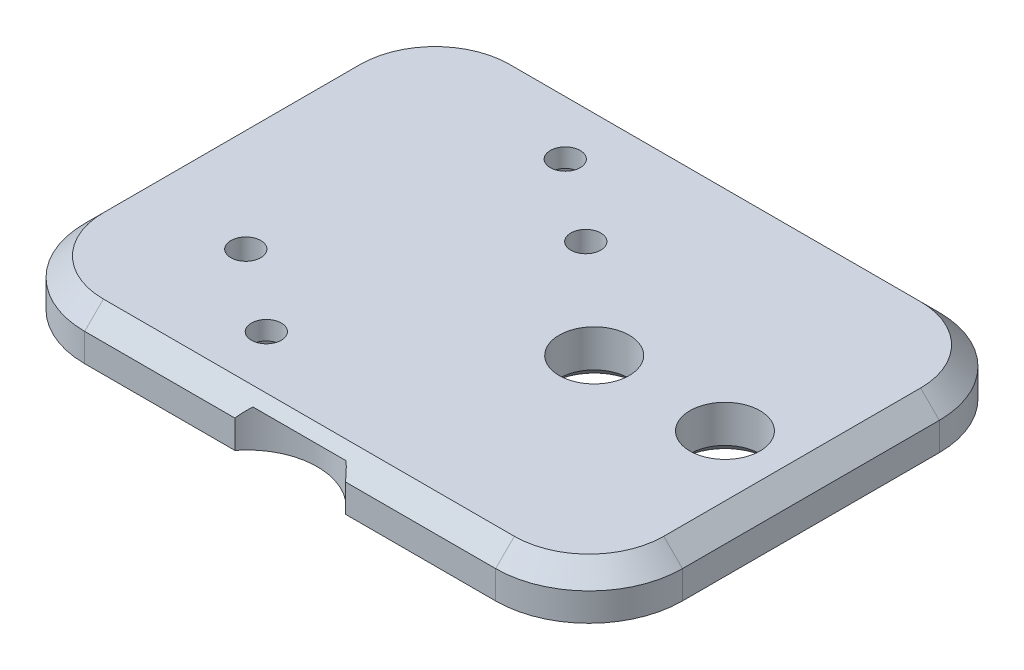
SolidWorks part; units mm, degrees
ref_plane "Front Plane" through (0, 0, 0) normal (0, 0, 1) x (1, 0, 0)
ref_plane "Top Plane" through (0, 0, 0) normal (0, 1, 0) x (1, 0, 0)
ref_plane "Right Plane" through (0, 0, 0) normal (1, 0, 0) x (0, 0, -1)
sketch "Sketch1" plane through (0, 0, 0) normal (0, 1, 0) x (1, 0, 0)
  line L0 (-37.5919, -19.2294) -> (-37.5919, -66.7294) construction
  line L1 (-69.5919, -19.2294) -> (-5.5919, -19.2294)
  line L2 (-69.5919, -19.2294) -> (-69.5919, -66.7294)
  line L3 (-69.5919, -66.7294) -> (-5.5919, -66.7294)
  line L4 (-5.5919, -19.2294) -> (-5.5919, -66.7294)
  line L5 (-69.5919, -19.2294) -> (-5.5919, -66.7294) construction
  line L6 (-69.5919, -66.7294) -> (-5.5919, -19.2294) construction
  line L8 (-59.5919, -19.2294) -> (-15.5919, -19.2294) construction
  line L9 (-5.5919, -29.2294) -> (-5.5919, -66.7294) construction
  circle A0 centre (-39.0919, -33.5794) radius 1.6
  circle A1 centre (-56.5919, -52.4794) radius 1.6
  circle A2 centre (-28.0919, -43.6794) radius 3.75
  circle A3 centre (-14.0919, -43.6794) radius 3.75
  point P0 (0, 0)
  dimension "D1" = 3.2
  dimension "D2" = 3.2
  dimension "D3" = 7.5
  dimension "D4" = 7.5
extrude "Boss-Extrude1" add sketch "Sketch1" along normal blind 5
sketch "Sketch2" plane through (0, 0, 0) normal (0, -1, 0) x (1, 0, 0)
  line L0 (-47.8419, 59.0294) -> (-47.8419, 27.0294) construction
  line L1 (-56.5919, 52.4794) -> (-39.0919, 33.5794) construction
  line L2 (-5.5919, 43.6794) -> (-69.5919, 43.6794) construction
  line L3 (-5.5919, 66.7294) -> (-5.5919, 19.2294) construction
  line L4 (-69.5919, 19.2294) -> (-69.5919, 66.7294) construction
  line L5 (-29.5919, 43.6794) -> (-26.5919, 43.6794) construction
  line L6 (-52.8419, 22.0294) -> (-42.8419, 22.0294) construction
  line L7 (-52.8419, 22.0294) -> (-52.8419, 64.0294) construction
  line L8 (-52.8419, 64.0294) -> (-42.8419, 64.0294) construction
  line L9 (-42.8419, 22.0294) -> (-42.8419, 64.0294) construction
  line L10 (-52.8419, 22.0294) -> (-42.8419, 64.0294) construction
  line L11 (-52.8419, 64.0294) -> (-42.8419, 22.0294) construction
  circle A0 centre (-47.8419, 59.0294) radius 1.6
  circle A3 centre (-47.8419, 27.0294) radius 1.6
  circle A4 centre (-28.0919, 43.6794) radius 1.5 construction
  point P5 (-47.8419, 43.0294)
  dimension "D1" = 3.2
  dimension "D2" = 10
  dimension "D3" = 5
  dimension "D4" = 3.2
  dimension "D5" = 32
extrude "Cut-Extrude1" cut sketch "Sketch2" against normal through all
sketch "Sketch3" plane through (0, 0, 0) normal (0, -1, 0) x (-1, 0, 0)
  line L1 (49.4296, -56.2794) -> (46.2542, -56.2794)
  line L2 (46.2542, -56.2794) -> (44.6665, -59.0294)
  line L3 (44.6665, -59.0294) -> (46.2542, -61.7794)
  line L4 (46.2542, -61.7794) -> (49.4296, -61.7794)
  line L5 (49.4296, -61.7794) -> (51.0173, -59.0294)
  line L6 (51.0173, -59.0294) -> (49.4296, -56.2794)
  line L18 (46.2542, -29.7794) -> (49.4296, -29.7794)
  line L19 (49.4296, -29.7794) -> (51.0173, -27.0294)
  line L20 (51.0173, -27.0294) -> (49.4296, -24.2794)
  line L21 (49.4296, -24.2794) -> (46.2542, -24.2794)
  line L22 (46.2542, -24.2794) -> (44.6665, -27.0294)
  line L23 (44.6665, -27.0294) -> (46.2542, -29.7794)
  line L30 (34.5919, -44.6171) -> (34.5919, -41.4417) [skipped]
  line L31 (34.5919, -41.4417) -> (31.8419, -39.854) [skipped]
  line L32 (31.8419, -39.854) -> (29.0919, -41.4417) [skipped]
  line L33 (29.0919, -41.4417) -> (29.0919, -44.6171) [skipped]
  line L34 (29.0919, -44.6171) -> (31.8419, -46.2048) [skipped]
  line L35 (31.8419, -46.2048) -> (34.5919, -44.6171) [skipped]
  line L36 (61.0919, -41.4417) -> (61.0919, -44.6171) [skipped]
  line L37 (61.0919, -44.6171) -> (63.8419, -46.2048) [skipped]
  line L38 (63.8419, -46.2048) -> (66.5919, -44.6171) [skipped]
  line L39 (66.5919, -44.6171) -> (66.5919, -41.4417) [skipped]
  line L40 (66.5919, -41.4417) -> (63.8419, -39.854) [skipped]
  line L41 (63.8419, -39.854) -> (61.0919, -41.4417) [skipped]
  circle A0 centre (47.8419, -59.0294) radius 2.75 construction
  circle A2 centre (47.8419, -27.0294) radius 2.75 construction
  circle A3 centre (47.8419, -27.0294) radius 1.6 construction
  circle A5 centre (31.8419, -43.0294) radius 2.75 construction
  circle A6 centre (63.8419, -43.0294) radius 2.75 construction
  dimension "D2" = 5.5
  dimension "D1" = 4
extrude "Cut-Extrude2" cut sketch "Sketch3" against normal blind 3
fillet "Fillet1" radius 10 2 edges at (-5.5919, 2.5, 19.2294) (-69.5919, 2.5, 19.2294)
fillet "Fillet2" radius 10 2 edges at (-5.5919, 2.5, 66.7294) (-69.5919, 2.5, 66.7294)
chamfer "Chamfer1" distance 2 angle 45 8 edges at (-5.5919, 5, 42.9794) (-69.5919, 5, 42.9794) (-8.5209, 5, 22.1583) (-66.663, 5, 22.1583) (-37.5919, 5, 19.2294) (-37.5919, 5, 66.7294) (-8.5209, 5, 63.8005) (-66.663, 5, 63.8005)
chamfer "Chamfer2" distance 1 angle 45 2 edges at (-28.0919, 0, 47.4294) (-14.0919, 0, 47.4294)
sketch "Sketch4" plane through (0, 0, 0) normal (0, 1, 0) x (1, 0, 0)
  line L0 (-37.5919, -19.2294) -> (-37.5919, -66.7294) construction
  line L1 (-15.5919, -19.2294) -> (-59.5919, -19.2294) construction
  line L2 (-59.5919, -66.7294) -> (-15.5919, -66.7294) construction
  circle A0 centre (-57.5919, -31.1294) radius 5.25
  circle A1 centre (-17.5919, -31.1294) radius 5.25
  circle A2 centre (-37.5919, -71.3294) radius 7.5
  dimension "D1" = 10.5
  dimension "D2" = 15
extrude "Cut-Extrude3" cut sketch "Sketch4" along normal blind 4
